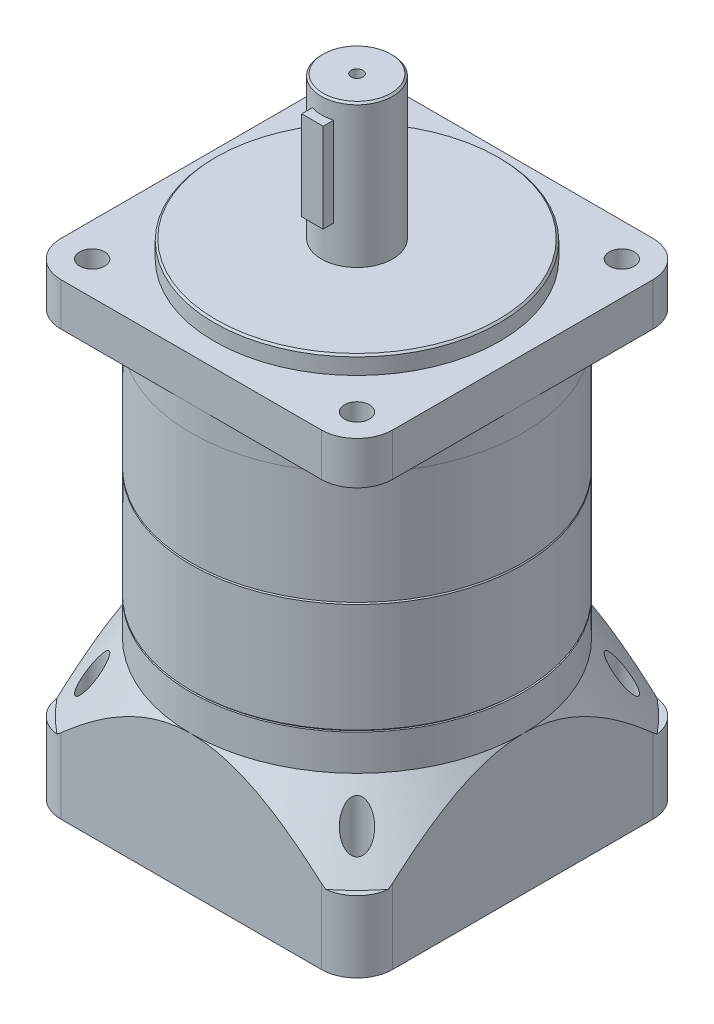
SolidWorks part; units mm, degrees
ref_plane "前基準面" through (0, 0, 0) normal (0, 0, 1) x (1, 0, 0)
ref_plane "上基準面" through (0, 0, 0) normal (0, 1, 0) x (1, 0, 0)
ref_plane "右基準面" through (0, 0, 0) normal (1, 0, 0) x (0, 0, -1)
sketch "草圖1" plane through (0, 0, 0) normal (0, 1, 0) x (1, 0, 0)
  line L1 (-36.5, -46.5) -> (36.5, -46.5)
  line L2 (-46.5, -36.5) -> (-46.5, 36.5)
  line L3 (-36.5, 46.5) -> (36.5, 46.5)
  line L4 (46.5, -36.5) -> (46.5, 36.5)
  line L5 (-46.5, -46.5) -> (46.5, 46.5) construction
  line L6 (-46.5, 46.5) -> (46.5, -46.5) construction
  arc A0 (36.5, -46.5) -> (46.5, -36.5) centre (36.5, -36.5) ccw
  arc A1 (-36.5, -46.5) -> (-46.5, -36.5) centre (-36.5, -36.5) cw
  arc A2 (36.5, 46.5) -> (46.5, 36.5) centre (36.5, 36.5) cw
  arc A3 (-46.5, 36.5) -> (-36.5, 46.5) centre (-36.5, 36.5) cw
  point P0 (0, 0)
  dimension "D3" = 10
  dimension "D1" = 93
  dimension "D2" = 93
extrude "填料-伸長1" add sketch "草圖1" along normal blind 49
sketch "草圖2" plane through (0, 49, 0) normal (0, 1, 0) x (1, 0, 0)
  circle A0 centre (0, 0) radius 46.5
extrude "除料-伸長3" cut sketch "草圖2" along normal blind 10 and the other way blind 19 draft 35 from offset 10 flip side to cut offset against normal yes
sketch "草圖3" plane through (0, 49, 0) normal (0, 1, 0) x (1, 0, 0)
  circle A0 centre (0, 0) radius 46.5
extrude "填料-伸長2" add sketch "草圖3" along normal blind 31.5 separate body
sketch "草圖18" plane through (0, 80.5, 0) normal (0, 1, 0) x (1, 0, 0)
  circle A0 centre (0, 0) radius 46.5
extrude "填料-伸長9" add sketch "草圖18" along normal blind 31.5 separate body
sketch "草圖4" plane through (0, 112, 0) normal (0, 1, 0) x (1, 0, 0)
  circle A0 centre (0, 0) radius 46.5
extrude "填料-伸長3" add sketch "草圖4" along normal blind 19 separate body
chamfer "導角1" distance 0.5 angle 45 2 edges at (0, 80.5, 46.5) (0, 49, 46.5)
sketch "草圖6" plane through (0, 131, 0) normal (0, 1, 0) x (1, 0, 0)
  circle A0 centre (0, 0) radius 40
  dimension "D1" = 80
extrude "填料-伸長5" add sketch "草圖6" along normal blind 5
sketch "草圖7" plane through (0, 136, 0) normal (0, 1, 0) x (1, 0, 0)
  circle A0 centre (0, 0) radius 10
  dimension "D1" = 20
extrude "填料-伸長6" add sketch "草圖7" along normal blind 40
chamfer "導角2" distance 0.5 angle 45 3 edges at (0, 176, 10) (0, 131, 46.5) (0, 136, 40)
sketch "草圖10" plane through (0, 0, 0) normal (0, 0, 1) x (1, 0, 0)
  line L0 (9.5, 176) -> (-9.5, 176) construction
  line L1 (-3, 171) -> (3, 171)
  line L2 (-3, 171) -> (-3, 146)
  line L3 (-3, 146) -> (3, 146)
  line L4 (3, 171) -> (3, 146)
  line L5 (0, -51.15) -> (0, 51.15) construction
  dimension "D1" = 5
  dimension "D2" = 6
  dimension "D3" = 3
  dimension "D4" = 25
extrude "填料-伸長7" add sketch "草圖10" along normal blind 12.5
sketch "草圖11" plane through (0, 0, 0) normal (0, -1, 0) x (1, 0, 0)
  circle A0 centre (0, 0) radius 35
  dimension "D1" = 70
extrude "除料-伸長4" cut sketch "草圖11" against normal blind 6
sketch "草圖12" plane through (0, 6, 0) normal (0, -1, 0) x (1, 0, 0)
  circle A0 centre (0, 0) radius 10
  dimension "D1" = 20
extrude "除料-伸長5" cut sketch "草圖12" against normal blind 40
hole_wizard "M4x0.7 螺紋孔1" positions "草圖14" profile "草圖13" tap size "M4x0.7" standard "JIS"
sketch "草圖14" plane through (0, 176, 0) normal (0, 1, 0) x (1, 0, 0)
  point P0 (0, 0)
sketch "草圖13" plane through (0, 176, 0) normal (1, 0, 0) x (0, 0, 1)
  line L0 (0, 0) -> (0, 11.0914)
  line L1 (0, 11.0914) -> (1.65, 10.1)
  line L2 (1.65, 10.1) -> (1.65, 0)
  line L5 (1.65, 0) -> (0, 0)
  line L10 (0, 11.0914) -> (-1.65, 10.1) construction
  line L11 (0, -6.35) -> (0, 107.95) construction
  dimension "螺孔鑽直徑" = 3.3
  dimension "螺孔鑽深度" = 10.1
  dimension "導頭角度" = 118
cosmetic thread "鑽孔螺紋2" parameters "D1"=8, "D2"=4
sketch "草圖15" plane through (0, 131, 0) normal (0, 1, 0) x (1, 0, 0)
  line L1 (-36.5, -46.5) -> (36.5, -46.5)
  line L2 (-46.5, -36.5) -> (-46.5, 36.5)
  line L3 (-36.5, 46.5) -> (36.5, 46.5)
  line L4 (46.5, -36.5) -> (46.5, 36.5)
  line L5 (-46.5, -46.5) -> (46.5, 46.5) construction
  line L6 (-46.5, 46.5) -> (46.5, -46.5) construction
  arc A0 (-36.5, -46.5) -> (-46.5, -36.5) centre (-36.5, -36.5) cw
  arc A1 (36.5, -46.5) -> (46.5, -36.5) centre (36.5, -36.5) ccw
  arc A2 (36.5, 46.5) -> (46.5, 36.5) centre (36.5, 36.5) cw
  arc A3 (-46.5, 36.5) -> (-36.5, 46.5) centre (-36.5, 36.5) cw
  circle A4 centre (0, 0) radius 44.7565
  point P0 (0, 0)
  dimension "D3" = 10
  dimension "D1" = 93
  dimension "D2" = 93
extrude "填料-伸長8" add sketch "草圖15" against normal blind 12
hole_wizard "Ø7.0 (7) 直徑孔3" positions "草圖17" profile "草圖16" hole size "Ø7.0" standard "JIS" end condition through all
sketch "草圖17" plane through (0, 131, 0) normal (0, 1, 0) x (1, 0, 0)
  line L0 (0, 0) -> (37.5471, 37.5471) construction
  line L3 (0, 0) -> (58.2659, 0) construction
  circle A0 centre (0, 0) radius 1.65 construction
  point P0 (37.1231, 37.1231)
  dimension "D1" = 52.5
  dimension "D2" = 45
sketch "草圖16" plane through (37.1231, 131, -37.1231) normal (1, 0, 0) x (0, 0, 1)
  line L0 (0, 0) -> (0, 131)
  line L1 (0, 131) -> (3.5, 131)
  line L2 (3.5, 131) -> (3.5, 0)
  line L5 (3.5, 0) -> (0, 0)
  line L11 (0, -6.35) -> (0, 107.95) construction
  dimension "貫穿孔直徑" = 7
  dimension "貫穿孔深度" = 131
pattern_circular "環狀複製排列1" count 4 over 360 about axis through (0, 0, 0) along (0, 1, 0) of "Ø7.0 (7) 直徑孔3"
